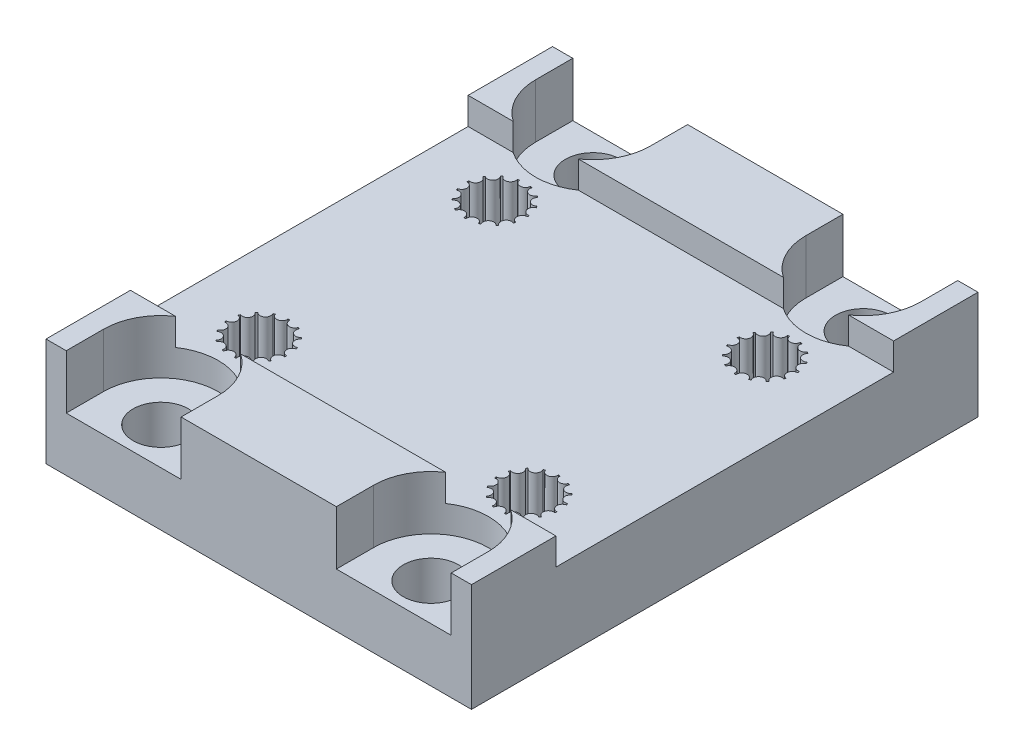
SolidWorks part; units mm, degrees
ref_plane "Front Plane" through (0, 0, 0) normal (0, 0, 1) x (1, 0, 0)
ref_plane "Top Plane" through (0, 0, 0) normal (0, 1, 0) x (1, 0, 0)
ref_plane "Right Plane" through (0, 0, 0) normal (1, 0, 0) x (0, 0, -1)
sketch "Sketch1" plane through (0, 0, 0) normal (0, 1, 0) x (1, 0, 0)
  line L0 (-20, 18.75) -> (20, 18.75)
  line L1 (-10, -8.75) -> (10, -8.75)
  line L2 (-10, -8.75) -> (-10, 8.75)
  line L3 (-10, 8.75) -> (10, 8.75)
  line L4 (10, -8.75) -> (10, 8.75)
  line L5 (-10, -8.75) -> (10, 8.75) construction
  line L6 (-10, 8.75) -> (10, -8.75) construction
  line L7 (20, -18.75) -> (20, 18.75)
  line L8 (-20, -18.75) -> (20, -18.75)
  line L9 (-20, -18.75) -> (-20, 18.75)
  point P0 (0, 0)
  dimension "D1" = 20
  dimension "D2" = 17.5
  dimension "D3" = 10
extrude "Boss-Extrude1" add sketch "Sketch1" along normal blind 8 contours L1 L4 L3 L2 | L9 L8 L7 L0 L4 L1 L2 L3
sketch "Sketch2" plane through (0, 8, 0) normal (0, 1, 0) x (1, 0, 0)
  circle A0 centre (-10, 8.75) radius 2.25
  circle A1 centre (-10, 11) radius 0.4
  circle A2 centre (-9.0848, 10.8055) radius 0.4
  circle A3 centre (-8.3279, 10.2555) radius 0.4
  circle A4 centre (-7.8601, 9.4453) radius 0.4
  circle A5 centre (-7.7623, 8.5148) radius 0.4
  circle A6 centre (-8.0514, 7.625) radius 0.4
  circle A7 centre (-8.6775, 6.9297) radius 0.4
  circle A8 centre (-9.5322, 6.5492) radius 0.4
  circle A9 centre (-10.4678, 6.5492) radius 0.4
  circle A10 centre (-11.3225, 6.9297) radius 0.4
  circle A11 centre (-11.9486, 7.625) radius 0.4
  circle A12 centre (-12.2377, 8.5148) radius 0.4
  circle A13 centre (-12.1399, 9.4453) radius 0.4
  circle A14 centre (-11.6721, 10.2555) radius 0.4
  circle A15 centre (-10.9152, 10.8055) radius 0.4
  point P35 (-10, 8.75)
  dimension "D1" = 4.5
  dimension "D2" = 0.8
  dimension "D3" = 15
extrude "Cut-Extrude1" cut sketch "Sketch2" against normal blind 10 contours A15 A0 A14 A13 A12 A11 A10 A9 A8 A7 A6 A5 A4 A3 A2 A1
ref_plane "Plane1" through (0, 0, 0) normal (-1, 0, 0) x (0, 0, 1)
ref_plane "Plane2" through (0, 0, 0) normal (0, 0, 1) x (1, 0, 0)
mirror "Mirror1" about plane through (0, 0, 0) normal (0, 0, 1) of "Cut-Extrude1" second plane through (0, 0, 0) second plane normal (-1, 0, 0)
sketch "Sketch3" plane through (0, 8, 0) normal (0, 1, 0) x (1, 0, 0)
  line L0 (-10, 16) -> (10, 16)
  line L1 (-10, -8.75) -> (10, -8.75)
  line L2 (-10, -8.75) -> (-10, 8.75)
  line L3 (-10, 8.75) -> (10, 8.75)
  line L4 (10, -8.75) -> (10, 8.75)
  line L5 (-10, -8.75) -> (10, 8.75) construction
  line L6 (-10, 8.75) -> (10, -8.75) construction
  line L7 (10, -16) -> (10, 16)
  line L8 (-10, -16) -> (10, -16)
  line L9 (-10, -16) -> (-10, 16)
  line L10 (-10, 0) -> (10, 0) construction
  circle A0 centre (-10, 16) radius 2.05
  point P0 (0, 0)
  dimension "D2" = 4.1
  dimension "D1" = 20
  dimension "D3" = 32
  dimension "D4" = 20
  dimension "D5" = 32
extrude "Cut-Extrude2" cut sketch "Sketch3" against normal blind 14 contours L0 A0 L9 | L9 A0 L0
mirror "Mirror2" about plane through (0, 0, 0) normal (0, 0, 1) of "Cut-Extrude2" second plane through (0, 0, 0) second plane normal (-1, 0, 0)
sketch "Sketch4" plane through (0, 8, 0) normal (0, 1, 0) x (1, 0, 0)
  line L0 (-14.25, 16) -> (-14.25, 18.75)
  line L1 (-20, 18.75) -> (20, 18.75) construction
  line L2 (-14.25, 18.75) -> (-5.75, 18.75)
  line L3 (-5.75, 18.75) -> (-5.75, 16)
  arc A0 (-14.25, 16) -> (-5.75, 16) centre (-10, 16) ccw
  dimension "D1" = 8.5
extrude "Cut-Extrude3" cut sketch "Sketch4" against normal blind 4
mirror "Mirror3" about plane through (0, 0, 0) normal (0, 0, 1) of "Cut-Extrude3" second plane through (0, 0, 0) second plane normal (-1, 0, 0)
sketch "Sketch5" plane through (0, 8, 0) normal (0, 1, 0) x (1, 0, 0)
  line L0 (30, 12.5) -> (30, 18.75)
  line L1 (-20, 18.75) -> (20, 18.75) construction
  line L2 (-30, -12.5) -> (30, -12.5)
  line L3 (-30, -12.5) -> (-30, 12.5)
  line L4 (-30, 12.5) -> (30, 12.5)
  line L5 (30, -12.5) -> (30, 12.5)
  line L6 (-30, -12.5) -> (30, 12.5) construction
  line L7 (-30, 12.5) -> (30, -12.5) construction
  point P2 (0, 0)
  dimension "D1" = 25
  dimension "D2" = 60
extrude "Cut-Extrude4" cut sketch "Sketch5" against normal blind 2 contours L2 L5 L4 L3
sketch "Sketch8" plane through (0, 6, 0) normal (0, 1, 0) x (1, 0, 0)
  line L0 (-20, -18.75) -> (20, -18.75) construction
  line L1 (-20, 18.75) -> (-15.75, 18.75)
  line L2 (-20, 18.75) -> (-20, -18.75)
  line L3 (-20, -18.75) -> (-15.75, -18.75)
  line L4 (-15.75, 18.75) -> (-15.75, -18.75)
  line L5 (-14.25, 18.75) -> (-14.25, 16) construction
  dimension "D1" = 1.5
extrude "Cut-Extrude5" cut sketch "Sketch8" against normal blind 18 and the other way blind 18
mirror "Mirror4" about plane through (0, 0, 0) normal (-1, 0, 0) of "Cut-Extrude5"
